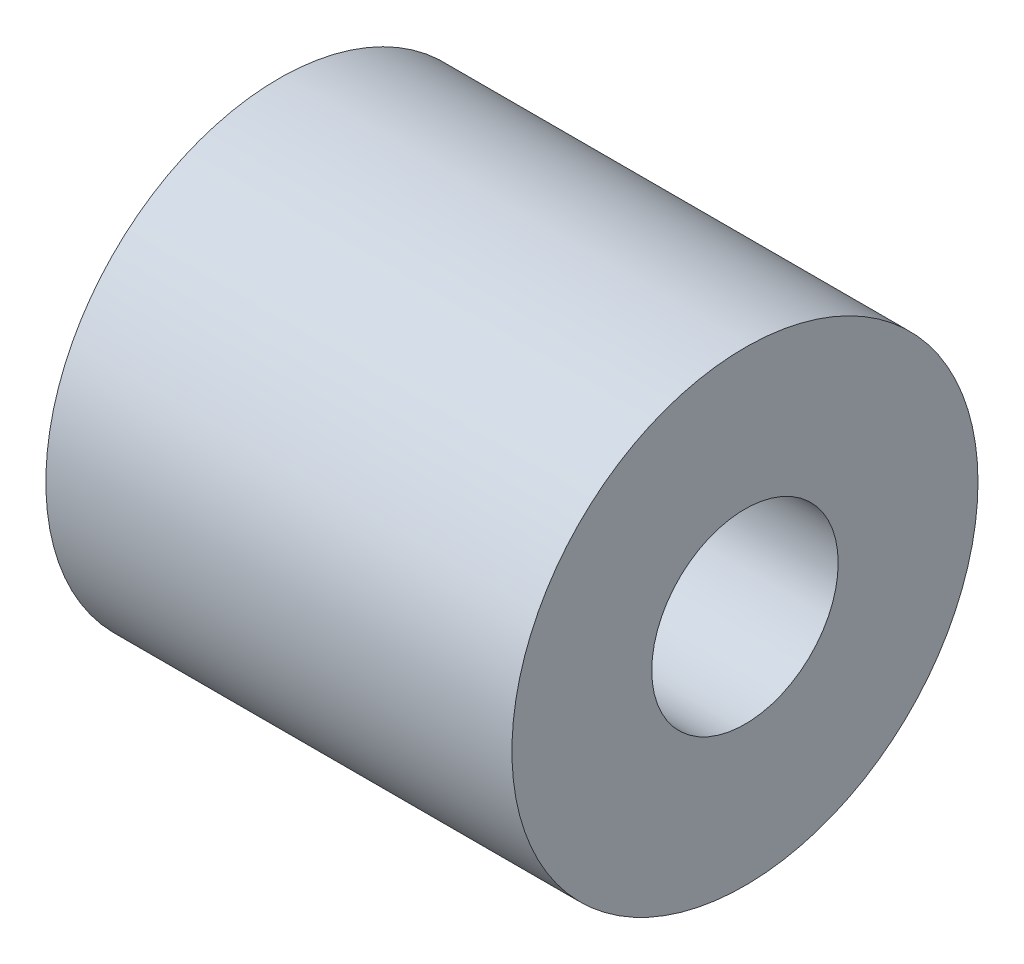
SolidWorks part; units mm, degrees
ref_plane "Front Plane" through (0, 0, 0) normal (0, 0, 1) x (1, 0, 0)
ref_plane "Top Plane" through (0, 0, 0) normal (0, 1, 0) x (1, 0, 0)
ref_plane "Right Plane" through (0, 0, 0) normal (1, 0, 0) x (0, 0, -1)
sketch "Sketch2" plane through (0, 0, 0) normal (1, 0, 0) x (0, 0, -1)
  circle A0 centre (0, 0) radius 5
  circle A1 centre (0, 0) radius 2
  dimension "D1" = 10
  dimension "D2" = 4
extrude "Boss-Extrude1" add sketch "Sketch2" along normal blind 10
